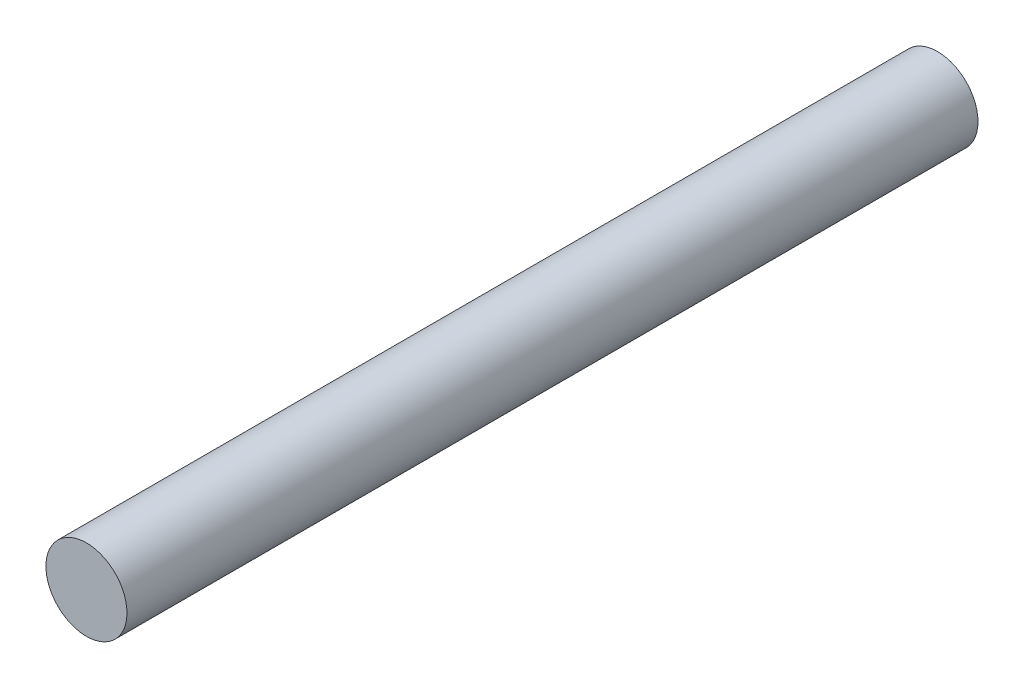
SolidWorks part; units mm, degrees
ref_plane "Front Plane" through (0, 0, 0) normal (0, 0, 1) x (1, 0, 0)
ref_plane "Top Plane" through (0, 0, 0) normal (0, 1, 0) x (1, 0, 0)
ref_plane "Right Plane" through (0, 0, 0) normal (1, 0, 0) x (0, 0, -1)
sketch "Sketch1" plane through (0, 0, 0) normal (0, 0, 1) x (1, 0, 0)
  circle A0 centre (0, 0) radius 3
  dimension "D1" = 6
extrude "Boss-Extrude1" add sketch "Sketch1" along normal blind 63
